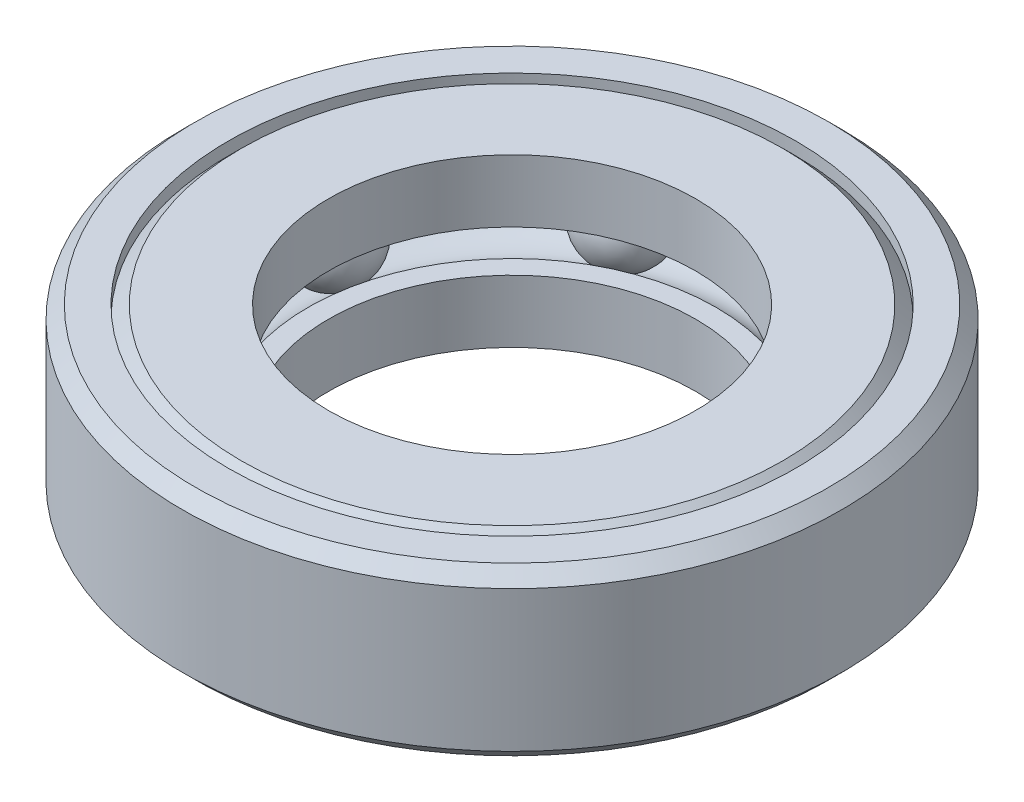
SolidWorks part; units mm, degrees
ref_plane "Front Plane" through (0, 0, 0) normal (0, 0, 1) x (1, 0, 0)
ref_plane "Top Plane" through (0, 0, 0) normal (0, 1, 0) x (1, 0, 0)
ref_plane "Right Plane" through (0, 0, 0) normal (1, 0, 0) x (0, 0, -1)
sketch "Sketch1" plane through (0, 0, 0) normal (1, 0, 0) x (0, 0, -1)
  line L0 (31.3531, 0) -> (-31.3531, 0) construction
  line L1 (0, -7.9375) -> (0, 7.9375) construction
  line L2 (-17.4625, 1.9844) -> (-17.4625, 7.9375) construction
  line L3 (-28.2178, 0) -> (-26.8089, 0) construction
  line L4 (-18.8714, 0) -> (-17.4625, 0) construction
  line L5 (-22.8402, 0) -> (-22.8402, 3.9688) construction
  line L6 (-17.4625, 1.9844) -> (-19.4031, 1.9844) construction
  line L7 (-26.2772, 1.9844) -> (-28.2178, 1.9844) construction
  line L8 (-28.2178, 1.9844) -> (-28.2178, 5.4716) construction
  line L9 (-28.2178, 5.4716) -> (-25.7519, 7.9375) construction
  line L10 (-25.7519, 7.9375) -> (-17.4625, 7.9375) construction
  line L11 (-25.7519, -7.9375) -> (-17.4625, -7.9375) construction
  line L12 (-28.2178, -5.4716) -> (-25.7519, -7.9375) construction
  line L13 (-28.2178, -1.9844) -> (-28.2178, -5.4716) construction
  line L14 (-26.2772, -1.9844) -> (-28.2178, -1.9844) construction
  line L15 (-17.4625, -1.9844) -> (-19.4031, -1.9844) construction
  line L16 (-17.4625, -1.9844) -> (-17.4625, -7.9375) construction
  line L17 (-17.4625, 7.9375) -> (-17.4625, -7.9375)
  line L18 (17.4625, 7.9375) -> (17.4625, -7.9375)
  line L19 (-25.7519, 7.9375) -> (25.7519, 7.9375) construction
  line L20 (-25.7519, -7.9375) -> (25.7519, -7.9375) construction
  circle A0 centre (-22.8402, 0) radius 3.9688 construction
  point P0 (-17.4625, 0)
  point P4 (0, 0)
  point P8 (0, 0)
  point P14 (-28.2178, 0)
  point P18 (-22.8402, 1.9844)
  point P23 (-22.8402, -1.9844)
  point P35 (-17.4625, 0)
  dimension "D1" = 7.9375
  dimension "OD" = 62.7063
  dimension "ID" = 34.925
  dimension "D2" = 56.4356
  dimension "D3" = 45
  dimension "Thickness" = 15.875
sketch "Sketch2" plane through (0, 0, 0) normal (1, 0, 0) x (0, 0, -1)
  line L0 (-26.2772, 1.9844) -> (-28.2178, 1.9844)
  line L1 (-28.2178, 1.9844) -> (-28.2178, 5.4716)
  line L2 (-28.2178, 5.4716) -> (-25.7519, 7.9375)
  line L3 (-25.7519, 7.9375) -> (-17.4625, 7.9375)
  line L4 (-17.4625, 7.9375) -> (-17.4625, 1.9844)
  line L5 (-17.4625, 1.9844) -> (-19.4031, 1.9844)
  line L6 (31.3531, 0) -> (-31.3531, 0) construction
  line L7 (31.3531, 0) -> (-31.3531, 0) construction
  line L8 (-17.4625, -1.9844) -> (-19.4031, -1.9844)
  line L9 (-17.4625, -7.9375) -> (-17.4625, -1.9844)
  line L10 (-25.7519, -7.9375) -> (-17.4625, -7.9375)
  line L11 (-28.2178, -5.4716) -> (-25.7519, -7.9375)
  line L12 (-28.2178, -1.9844) -> (-28.2178, -5.4716)
  line L13 (-26.2772, -1.9844) -> (-28.2178, -1.9844)
  arc A0 (-26.2772, 1.9844) -> (-19.4031, 1.9844) centre (-22.8402, 0) cw
  circle A1 centre (-22.8402, 0) radius 3.9688 construction
  arc A2 (-26.2772, -1.9844) -> (-19.4031, -1.9844) centre (-22.8402, 0) ccw
revolve "Revolve1" add sketch "Sketch2" angle 360 about L1
sketch "Sketch3" plane through (0, 0, 0) normal (1, 0, 0) x (0, 0, -1)
  line L0 (-26.9849, 6.7046) -> (-26.9849, 7.9375)
  line L1 (-28.2178, 5.4716) -> (-25.7519, 7.9375) construction
  line L2 (-31.3531, 6.7046) -> (-30.1202, 7.9375)
  line L3 (-31.3531, 6.7046) -> (-31.3531, -6.7046)
  line L4 (-30.1202, 7.9375) -> (-26.9849, 7.9375)
  line L5 (-25.7519, 7.9375) -> (-17.4625, 7.9375) construction
  line L6 (31.3531, 0) -> (-31.3531, 0) construction
  line L7 (31.3531, 0) -> (-31.3531, 0) construction
  line L8 (-30.1202, -7.9375) -> (-26.9849, -7.9375)
  line L9 (-31.3531, -6.7046) -> (-30.1202, -7.9375)
  line L10 (-26.9849, -6.7046) -> (-26.9849, -7.9375)
  line L11 (-26.9849, 6.7046) -> (-28.2178, 5.4716)
  line L12 (-28.2178, 5.4716) -> (-28.2178, -5.4716)
  line L13 (-28.2178, -5.4716) -> (-26.9849, -6.7046)
revolve "Revolve2" add sketch "Sketch3" angle 360 about L1
sketch "Sketch4" plane through (0, 0, 0) normal (1, 0, 0) x (0, 0, -1)
  line L0 (-22.8402, 3.9688) -> (-22.8402, -3.9688)
  circle A0 centre (-22.8402, 0) radius 3.9688 construction
  arc A1 (-22.8402, -3.9688) -> (-22.8402, 3.9688) centre (-22.8402, 0) ccw
revolve "Revolve3" add sketch "Sketch4" angle 360 about L0
pattern_circular "CirPattern1" count 7 over 360 about axis through (0, 0, 0) along (0, 1, 0) of bodies 107
sketch "Sketch5" plane through (0, 0, 0) normal (1, 0, 0) x (0, 0, -1)
  line L0 (-19.4031, 1.9844) -> (-17.4625, 1.9844)
  line L1 (17.4625, 1.9844) -> (19.4031, 1.9844)
  line L2 (-17.4625, 1.9844) -> (-17.4625, 7.9375)
  line L3 (17.4625, 7.9375) -> (17.4625, 1.9844)
  line L4 (25.7519, 7.9375) -> (17.4625, 7.9375)
  line L5 (-17.4625, 7.9375) -> (-25.7519, 7.9375)
  line L6 (-25.7519, 7.9375) -> (-28.2178, 5.4716)
  line L7 (28.2178, 5.4716) -> (25.7519, 7.9375)
  line L8 (-28.2178, 5.4716) -> (-28.2178, 1.9844)
  line L9 (28.2178, 1.9844) -> (28.2178, 5.4716)
  line L10 (-28.2178, 1.9844) -> (-26.2772, 1.9844)
  line L11 (26.2772, 1.9844) -> (28.2178, 1.9844)
  line L12 (26.2772, 1.9844) -> (28.2178, 1.9844)
  line L13 (-28.2178, 1.9844) -> (-26.2772, 1.9844)
  line L14 (28.2178, 1.9844) -> (28.2178, 5.4716)
  line L15 (-28.2178, 5.4716) -> (-28.2178, 1.9844)
  line L16 (28.2178, 5.4716) -> (25.7519, 7.9375)
  line L17 (-25.7519, 7.9375) -> (-28.2178, 5.4716)
  line L18 (-17.4625, 7.9375) -> (-25.7519, 7.9375)
  line L19 (25.7519, 7.9375) -> (17.4625, 7.9375)
  line L20 (17.4625, 7.9375) -> (17.4625, 1.9844)
  line L21 (-17.4625, 1.9844) -> (-17.4625, 7.9375)
  line L22 (17.4625, 1.9844) -> (19.4031, 1.9844)
  line L23 (-19.4031, 1.9844) -> (-17.4625, 1.9844)
  line L24 (19.4031, -1.9844) -> (17.4625, -1.9844)
  line L25 (-17.4625, -1.9844) -> (-19.4031, -1.9844)
  line L26 (-17.4625, -7.9375) -> (-17.4625, -1.9844)
  line L27 (17.4625, -1.9844) -> (17.4625, -7.9375)
  line L28 (-25.7519, -7.9375) -> (-17.4625, -7.9375)
  line L29 (17.4625, -7.9375) -> (25.7519, -7.9375)
  line L30 (25.7519, -7.9375) -> (28.2178, -5.4716)
  line L31 (-28.2178, -5.4716) -> (-25.7519, -7.9375)
  line L32 (-28.2178, -1.9844) -> (-28.2178, -5.4716)
  line L33 (28.2178, -5.4716) -> (28.2178, -1.9844)
  line L34 (28.2178, -1.9844) -> (26.2772, -1.9844)
  line L35 (-26.2772, -1.9844) -> (-28.2178, -1.9844)
  line L36 (-26.2772, -1.9844) -> (-28.2178, -1.9844)
  line L37 (28.2178, -1.9844) -> (26.2772, -1.9844)
  line L38 (28.2178, -5.4716) -> (28.2178, -1.9844)
  line L39 (-28.2178, -1.9844) -> (-28.2178, -5.4716)
  line L40 (-28.2178, -5.4716) -> (-25.7519, -7.9375)
  line L41 (25.7519, -7.9375) -> (28.2178, -5.4716)
  line L42 (17.4625, -7.9375) -> (25.7519, -7.9375)
  line L43 (-25.7519, -7.9375) -> (-17.4625, -7.9375)
  line L44 (17.4625, -1.9844) -> (17.4625, -7.9375)
  line L45 (-17.4625, -7.9375) -> (-17.4625, -1.9844)
  line L46 (-17.4625, -1.9844) -> (-19.4031, -1.9844)
  line L47 (19.4031, -1.9844) -> (17.4625, -1.9844)
  line L48 (-28.2178, -5.4716) -> (-28.2178, 5.4716)
  line L49 (28.2178, 5.4716) -> (28.2178, -5.4716)
  line L50 (28.2178, -5.4716) -> (26.9849, -6.7046)
  line L51 (-26.9849, -6.7046) -> (-28.2178, -5.4716)
  line L52 (-12.8207, -7.1438) -> (-26.9849, -6.7046)
  line L53 (26.9849, -6.7046) -> (12.8207, -7.1438)
  line L54 (-14.3685, -7.1438) -> (-12.8207, -7.1438)
  line L55 (12.8207, -7.1438) -> (14.3685, -7.1438)
  line L56 (14.3685, -7.1438) -> (15.4781, -6.0341)
  line L57 (-15.4781, -6.0341) -> (-14.3685, -7.1438)
  line L58 (-15.4781, 6.0341) -> (-15.4781, -6.0341)
  line L59 (15.4781, -6.0341) -> (15.4781, 6.0341)
  line L60 (-14.3685, 7.1438) -> (-15.4781, 6.0341)
  line L61 (15.4781, 6.0341) -> (30.1202, 7.9375)
  line L62 (30.1202, 7.9375) -> (26.9849, 7.9375)
  line L63 (-12.8207, 7.1438) -> (-14.3685, 7.1438)
  line L64 (-26.9849, 6.7046) -> (-12.8207, 7.1438)
  line L65 (26.9849, 7.9375) -> (26.9849, 6.7046)
  line L66 (-28.2178, 5.4716) -> (-26.9849, 6.7046)
  line L67 (26.9849, 6.7046) -> (28.2178, 5.4716)
  line L68 (26.9849, 6.7046) -> (28.2178, 5.4716)
  line L69 (-28.2178, 5.4716) -> (-26.9849, 6.7046)
  line L73 (30.1202, 7.9375) -> (26.9849, 7.9375)
  line L84 (-26.9849, -6.7046) -> (-28.2178, -5.4716)
  line L85 (28.2178, -5.4716) -> (26.9849, -6.7046)
  line L86 (28.2178, 5.4716) -> (28.2178, -5.4716)
  line L87 (-28.2178, -5.4716) -> (-28.2178, 5.4716)
  line L88 (-17.4625, 7.9375) -> (17.4625, 7.9375)
  line L89 (-17.4625, 1.9844) -> (17.4625, 1.9844)
  line L90 (17.4625, -1.9844) -> (-17.4625, -1.9844)
  line L91 (-17.4625, -7.9375) -> (17.4625, -7.9375)
  arc A0 (-19.4031, 1.9844) -> (-26.2772, 1.9844) centre (-22.8402, 0) ccw
  arc A1 (26.2772, 1.9844) -> (19.4031, 1.9844) centre (22.8402, 0) ccw
  arc A2 (26.2772, 1.9844) -> (19.4031, 1.9844) centre (22.8402, 0) ccw
  arc A3 (-19.4031, 1.9844) -> (-26.2772, 1.9844) centre (-22.8402, 0) ccw
  arc A4 (-26.2772, -1.9844) -> (-19.4031, -1.9844) centre (-22.8402, 0) ccw
  arc A5 (19.4031, -1.9844) -> (26.2772, -1.9844) centre (22.8402, 0) ccw
  arc A6 (19.4031, -1.9844) -> (26.2772, -1.9844) centre (22.8402, 0) ccw
  arc A7 (-26.2772, -1.9844) -> (-19.4031, -1.9844) centre (-22.8402, 0) ccw
  circle A9 centre (22.8402, 0) radius 3.9688
  circle A10 centre (-22.8402, 0) radius 3.9688
  circle A11 centre (-22.8402, 0) radius 3.9688
sketch "Sketch6" plane through (0, 0, 0) normal (0, 1, 0) x (1, 0, 0)
  circle A0 centre (0, 0) radius 31.3531
  circle A1 centre (0, 0) radius 17.4625
  dimension "OD Toleranced" = 62.7063
  dimension "For Shaft Diameter for Drawing" = 34.925
equation "\"D1@Sketch1\"=\"Thickness@Sketch1\"/2"
equation "\"D2@Sketch1\"=\"OD@Sketch1\"*.9"
equation "\"D1@CirPattern1\"=\"OD@Sketch1\"*3"
